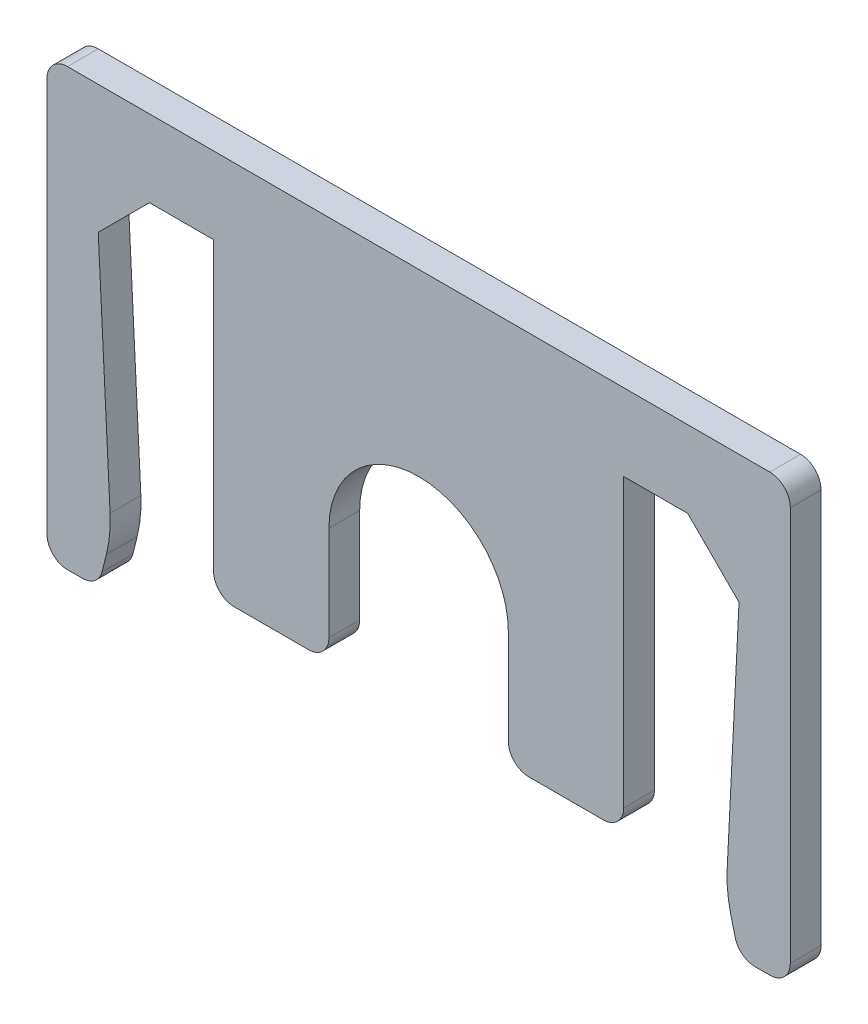
SolidWorks part; units mm, degrees
ref_plane "Front Plane" through (0, 0, 0) normal (0, 0, 1) x (1, 0, 0)
ref_plane "Top Plane" through (0, 0, 0) normal (0, 1, 0) x (1, 0, 0)
ref_plane "Right Plane" through (0, 0, 0) normal (1, 0, 0) x (0, 0, -1)
sketch "Sketch1" plane through (0, 0, 0) normal (0, 0, 1) x (1, 0, 0)
  line L0 (-12.5, 0) -> (-10.5, 0) construction
  line L1 (-10.5, 0) -> (-12.5, -2)
  line L2 (-12.5, -2) -> (-12.5, 0) construction
  line L3 (12.5, 0) -> (12.5, -2) construction
  line L4 (12.5, -2) -> (10.5, 0)
  line L5 (10.5, 0) -> (12.5, 0) construction
  line L6 (-12.5, -2) -> (-12, -12)
  line L7 (-12, -12) -> (-12.5, -14)
  line L8 (-12.5, -14) -> (-12.5, -2) construction
  line L9 (12.5, -2) -> (12.5, -14) construction
  line L10 (12.5, -14) -> (12, -12)
  line L11 (12, -12) -> (12.5, -2)
  line L12 (-10.5, 0) -> (-8, 0) construction
  line L13 (-3.5, -12) -> (3.5, -12) construction
  line L14 (-12.5, -14) -> (-14.5, -14)
  line L15 (-12.5, -14) -> (-12.5, -2) construction
  line L16 (-12.5, 3) -> (-14.5, 3)
  line L17 (-14.5, -14) -> (-14.5, 3)
  line L18 (12.5, -14) -> (14.5, -14)
  line L19 (12.5, -14) -> (12.5, -2) construction
  line L20 (12.5, 3) -> (14.5, 3)
  line L21 (14.5, -14) -> (14.5, 3)
  line L22 (-12.5, 3) -> (12.5, 3)
  line L23 (-12.5, 3) -> (-12.5, 0) construction
  line L24 (-10.5, 0) -> (-8, 0)
  line L25 (12.5, 3) -> (12.5, 0) construction
  line L26 (-3.5, -7.5) -> (3.5, -7.5) construction
  line L27 (-3.5, -7.5) -> (-3.5, -12)
  line L28 (-3.5, -12) -> (3.5, -12) construction
  line L29 (3.5, -7.5) -> (3.5, -12)
  line L30 (-8, -12) -> (-3.5, -12)
  line L31 (-8, -12) -> (-8, 0)
  line L32 (-8, 0) -> (8, 0) construction
  line L33 (8, -12) -> (8, 0)
  line L34 (-4.5, -3) -> (4.5, -3) construction
  line L35 (-4.5, -3) -> (-4.5, -12) construction
  line L36 (-4.5, -12) -> (-3.5, -12) construction
  line L37 (4.5, -3) -> (4.5, -12) construction
  line L38 (-4.5, -3) -> (4.5, -12) construction
  line L39 (-4.5, -12) -> (4.5, -3) construction
  line L40 (3.5, -12) -> (8, -12)
  line L41 (-3.5, -12) -> (3.5, -12) construction
  line L42 (3.5, -12) -> (4.5, -12) construction
  line L43 (-8, 0) -> (8, 0) construction
  line L44 (8, 0) -> (10.5, 0) construction
  line L45 (-8, 0) -> (8, 0) construction
  line L46 (8, 0) -> (10.5, 0)
  line L47 (-12.5, -2) -> (-12.5, 0) construction
  line L48 (-12.5, 0) -> (-12.5, 3) construction
  line L49 (-12.5, 0) -> (-10.5, 0) construction
  line L50 (12.5, 0) -> (12.5, 3) construction
  line L51 (10.5, 0) -> (12.5, 0) construction
  line L52 (12.5, -2) -> (12.5, 0) construction
  arc A0 (3.5, -7.5) -> (-3.5, -7.5) centre (0, -7.5) ccw
  arc A1 (-3.5, -7.5) -> (-2.4749, -9.9749) centre (0, -7.5) ccw construction
  arc A2 (-2.4749, -9.9749) -> (2.4749, -9.9749) centre (0, -7.5) ccw construction
  arc A3 (2.4749, -9.9749) -> (3.5, -7.5) centre (0, -7.5) ccw construction
  point P28 (0, 0)
  point P29 (0, -7.5)
  point P34 (5.8042, -3.4177)
  point P35 (-0.1925, -6.6497)
  point P37 (0, -6.898)
  point P38 (0, -7.5)
  point P39 (0, 0)
  dimension "D12" = 7
  dimension "D1" = 2
  dimension "D2" = 2
  dimension "D3" = 2
  dimension "D4" = 0.5
  dimension "D5" = 2
  dimension "D6" = 10
  dimension "D7" = 0.5
  dimension "D8" = 21
  dimension "D9" = 2
  dimension "D10" = 2
  dimension "D11" = 3
  dimension "D13" = 16
  dimension "D14" = 9
  dimension "D15" = 9
  dimension "D16" = 10.5
extrude "Boss-Extrude1" add sketch "Sketch1" along normal blind 1.2
fillet "Fillet1" radius 5 2 edges at (-12, -12, 0.6) (12, -12, 0.6)
fillet "Fillet2" radius 0.8 10 edges at (14.5, 3, 0.6) (-14.5, 3, 0.6) (14.5, -14, 0.6) (-14.5, -14, 0.6) (12.5, -14, 0.6) (-12.5, -14, 0.6) (-8, -12, 0.6) (8, -12, 0.6) (3.5, -12, 0.6) (-3.5, -12, 0.6)
